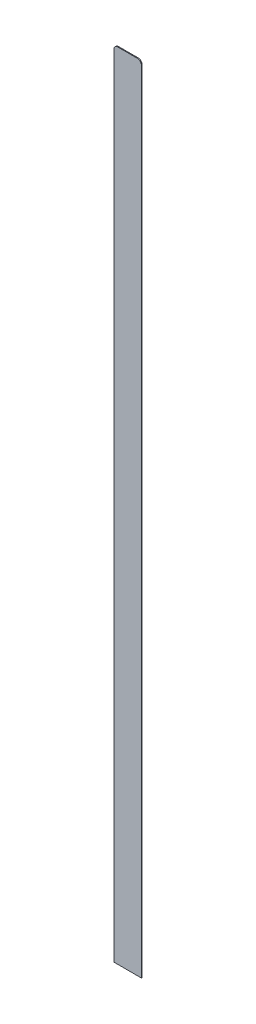
SolidWorks part; units mm, degrees
ref_plane "Plano frontal" through (0, 0, 0) normal (0, 0, 1) x (1, 0, 0)
ref_plane "Plano superior" through (0, 0, 0) normal (0, 1, 0) x (1, 0, 0)
ref_plane "Plano direito" through (0, 0, 0) normal (1, 0, 0) x (0, 0, -1)
sketch "Esboço1" plane through (0, 0, 0) normal (0, 0, 1) x (1, 0, 0)
  line L1 (0, 0) -> (35, 0)
  line L2 (0, 0) -> (0, 1010)
  line L3 (0, 1010) -> (35, 1010)
  line L4 (35, 0) -> (35, 1010)
  dimension "D1" = 1010
  dimension "D2" = 35
extrude "Ressalto-extrusão1" add sketch "Esboço1" along normal blind 1
fillet "Filete1" radius 5 2 edges at (35, 1010, 0.5) (0, 1010, 0.5)
